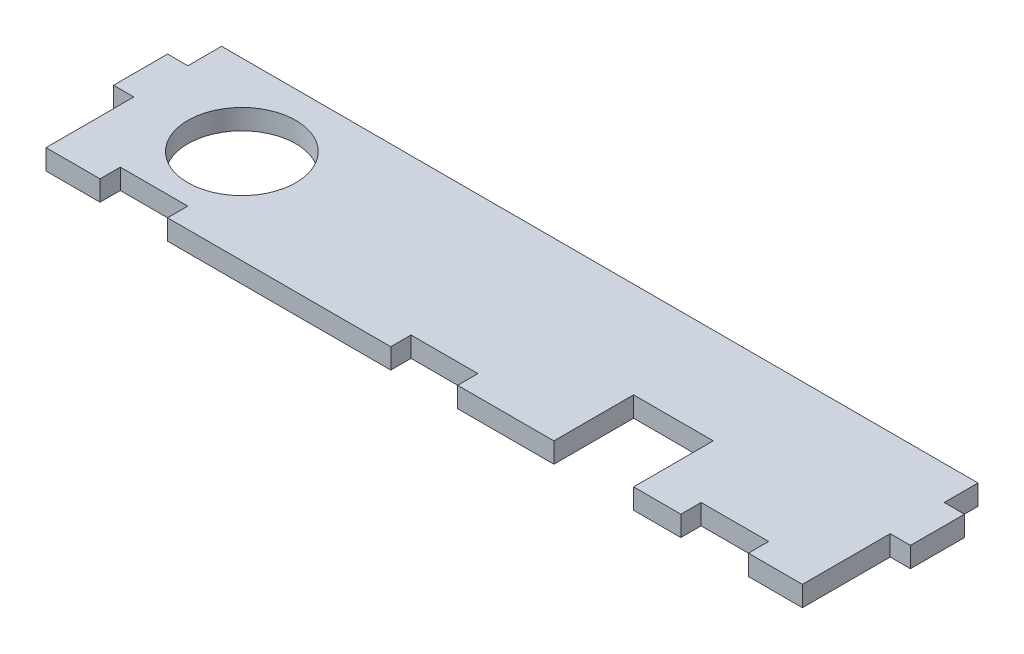
SolidWorks part; units mm, degrees
material "Acrylic (Medium-high impact)"
ref_plane "Front Plane" through (0, 0, 0) normal (0, 0, 1) x (1, 0, 0)
ref_plane "Top Plane" through (0, 0, 0) normal (0, 1, 0) x (1, 0, 0)
ref_plane "Right Plane" through (0, 0, 0) normal (1, 0, 0) x (0, 0, -1)
sketch "Sketch1" plane through (0, 0, 0) normal (0, 1, 0) x (1, 0, 0)
  line L0 (1213.4081, -2432.3937) -> (1216.4081, -2432.3937)
  line L1 (1101.4081, -2419.3937) -> (1213.4081, -2419.3937)
  line L2 (1109.4081, -2442.3937) -> (1109.4081, -2445.3937)
  line L3 (1119.4081, -2445.3937) -> (1152.4581, -2445.3937)
  line L4 (1213.4081, -2432.3937) -> (1213.4081, -2445.3937)
  line L5 (1216.4081, -2432.3937) -> (1216.4081, -2424.3937)
  line L6 (1195.4081, -2445.3937) -> (1195.4081, -2442.3937)
  line L7 (1216.4081, -2424.3937) -> (1213.4081, -2424.3937)
  line L8 (1213.4081, -2419.3937) -> (1213.4081, -2424.3937)
  line L9 (1195.4081, -2442.3937) -> (1205.4081, -2442.3937)
  line L10 (1119.4081, -2442.3937) -> (1109.4081, -2442.3937)
  line L11 (1101.4081, -2419.3937) -> (1101.4081, -2424.3937)
  line L12 (1098.4081, -2424.3937) -> (1101.4081, -2424.3937)
  line L13 (1119.4081, -2445.3937) -> (1119.4081, -2442.3937)
  line L14 (1098.4081, -2432.3937) -> (1098.4081, -2424.3937)
  line L15 (1101.4081, -2432.3937) -> (1101.4081, -2445.3937)
  line L16 (1101.4081, -2432.3937) -> (1098.4081, -2432.3937)
  line L17 (1109.4081, -2445.3937) -> (1101.4081, -2445.3937)
  line L18 (1205.4081, -2442.3937) -> (1205.4081, -2445.3937)
  line L19 (1205.4081, -2445.3937) -> (1213.4081, -2445.3937)
  line L22 (1188.4081, -2445.3937) -> (1195.4081, -2445.3937)
  line L23 (1152.4581, -2445.3937) -> (1152.4581, -2442.3937)
  line L24 (1152.4581, -2442.3937) -> (1162.3581, -2442.3937)
  line L28 (1162.3581, -2442.3937) -> (1162.3581, -2445.3937)
  line L29 (1162.3581, -2445.3937) -> (1176.6081, -2445.3937)
  line L34 (1176.6081, -2433.5937) -> (1176.6081, -2445.3937)
  line L35 (1176.6081, -2433.5937) -> (1188.4081, -2433.5937)
  line L36 (1188.4081, -2433.5937) -> (1188.4081, -2445.3937)
  circle A0 centre (1116.4081, -2431.3937) radius 8
  dimension "D8" = 16
  dimension "D1" = 26
  dimension "D2" = 12
  dimension "D3" = 3
  dimension "D4" = 8
  dimension "D5" = 5
  dimension "D6" = 13
  dimension "D7" = 3
  dimension "D9" = 18
  dimension "D10" = 9.9
  dimension "D11" = 112
  dimension "D12" = 3
  dimension "D13" = 54.05
  dimension "D14" = 11.8
  dimension "D15" = 13
  dimension "D16" = 3
  dimension "D17" = 7
  dimension "D18" = 10
  dimension "D19" = 5
  dimension "D20" = 10
  dimension "D21" = 8
  dimension "D22" = 8
extrude "Boss-Extrude1" add sketch "Sketch1" along normal blind 3
